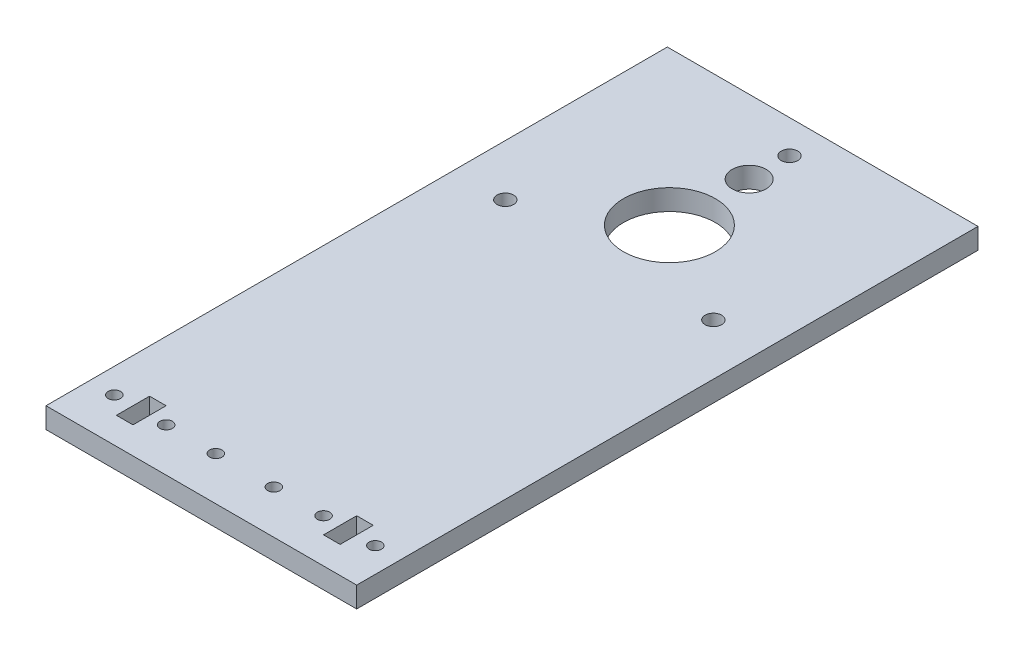
SolidWorks part; units mm, degrees
ref_plane "前视基准面" through (0, 0, 0) normal (0, 0, 1) x (1, 0, 0)
ref_plane "上视基准面" through (0, 0, 0) normal (0, 1, 0) x (1, 0, 0)
ref_plane "右视基准面" through (0, 0, 0) normal (1, 0, 0) x (0, 0, -1)
sketch "草图1" plane through (0, 0, 0) normal (0, 1, 0) x (1, 0, 0)
  line L0 (0, 0) -> (75, 0)
  line L1 (75, 0) -> (75, 150)
  line L2 (75, 150) -> (0, 150)
  line L3 (0, 150) -> (0, 0)
  line L4 (75, 0) -> (75, 11)
  line L6 (75, 8.5) -> (75, 10)
  line L12 (75, 0) -> (64.5, 0)
  line L14 (10.5, 6.5) -> (10.5, 10.5)
  line L15 (12.5, 6.5) -> (10.5, 6.5)
  line L18 (37.5, 11) -> (37.5, 0)
  line L24 (37.5, 150) -> (37.5, 113)
  line L25 (37.5, 113) -> (37.5, 93.75)
  line L26 (12.5, 14.5) -> (14.5, 14.5)
  line L27 (14.5, 14.5) -> (14.5, 6.5)
  line L28 (14.5, 6.5) -> (12.5, 6.5)
  line L40 (10.5, 10) -> (10.5, 12.5)
  line L42 (75, 10) -> (75, 10.5)
  line L43 (75, 10.5) -> (69, 10.5)
  line L44 (69, 10.5) -> (64.5, 10.5)
  line L45 (64.5, 10.5) -> (62.5, 10.5)
  line L46 (62.5, 10.5) -> (56.5, 10.5)
  line L47 (56.5, 10.5) -> (44.5, 10.5)
  line L48 (44.5, 10.5) -> (37.5, 10.5)
  line L49 (64.5, 10.5) -> (64.5, 14.5)
  line L50 (64.5, 14.5) -> (62.5, 14.5)
  line L51 (62.5, 14.5) -> (62.5, 10.5)
  line L52 (62.5, 10.5) -> (62.5, 6.5)
  line L53 (62.5, 6.5) -> (64.5, 6.5)
  line L54 (64.5, 6.5) -> (64.5, 10.5)
  line L55 (55.0858, 10) -> (56.5, 10)
  line L56 (12.5, 10.5) -> (12.5, 6.5)
  line L57 (12.5, 14.5) -> (12.5, 10.5)
  line L58 (10.5, 14.5) -> (12.5, 14.5)
  line L59 (10.5, 10.5) -> (10.5, 14.5)
  line L60 (37.5, 10.5) -> (75, 10.5)
  line L61 (75, 10.5) -> (75, 0)
  line L62 (37.5, 0) -> (75, 0)
  line L63 (62.5, 14.5) -> (60.5, 14.5)
  line L64 (60.5, 14.5) -> (60.5, 6.5)
  line L65 (60.5, 6.5) -> (62.5, 6.5)
  circle A6 centre (37.5, 113) radius 11.1
  circle A7 centre (37.5, 113) radius 19.25
  arc A8 (39.6873, 150) -> (35.3127, 150) centre (37.5, 113) ccw
  arc A11 (37.5, 150.0646) -> (39.6873, 150) centre (37.5, 113) cw
  circle A26 centre (69, 10.5) radius 1.5
  circle A27 centre (56.5, 10.5) radius 1.5
  circle A28 centre (44.5, 10.5) radius 1.5
  circle A29 centre (30.5, 10.5) radius 1.5
  circle A30 centre (18.5, 10.5) radius 1.5
  circle A31 centre (6, 10.5) radius 1.5
  circle A32 centre (37.5, 132.25) radius 4.1
  dimension "D1" = 8.5
  dimension "D2" = 37
extrude "凸台-拉伸6" add sketch "草图1" along normal blind 5
sketch "草图2" plane through (0, 5, 0) normal (0, 1, 0) x (1, 0, 0)
  line L0 (0, 150) -> (0, 0)
  line L1 (37.5, 132.25) -> (37.5, 113)
  line L2 (37.5, 132.25) -> (37.5, 142)
  circle A0 centre (37.5, 113) radius 11.1
  circle A1 centre (37.5, 132.25) radius 4.1
  circle A2 centre (37.5, 113) radius 29
  circle A3 centre (37.5, 142) radius 2
  circle A4 centre (62.6147, 98.5) radius 2
  circle A5 centre (12.3853, 98.5) radius 2
  point P19 (37.5, 113)
  dimension "D1" = 3
extrude "切除-拉伸1" cut sketch "草图2" against normal blind 10 contours A2 A5 | A2 A5 | A2 A4 | A2 A4 | A3
